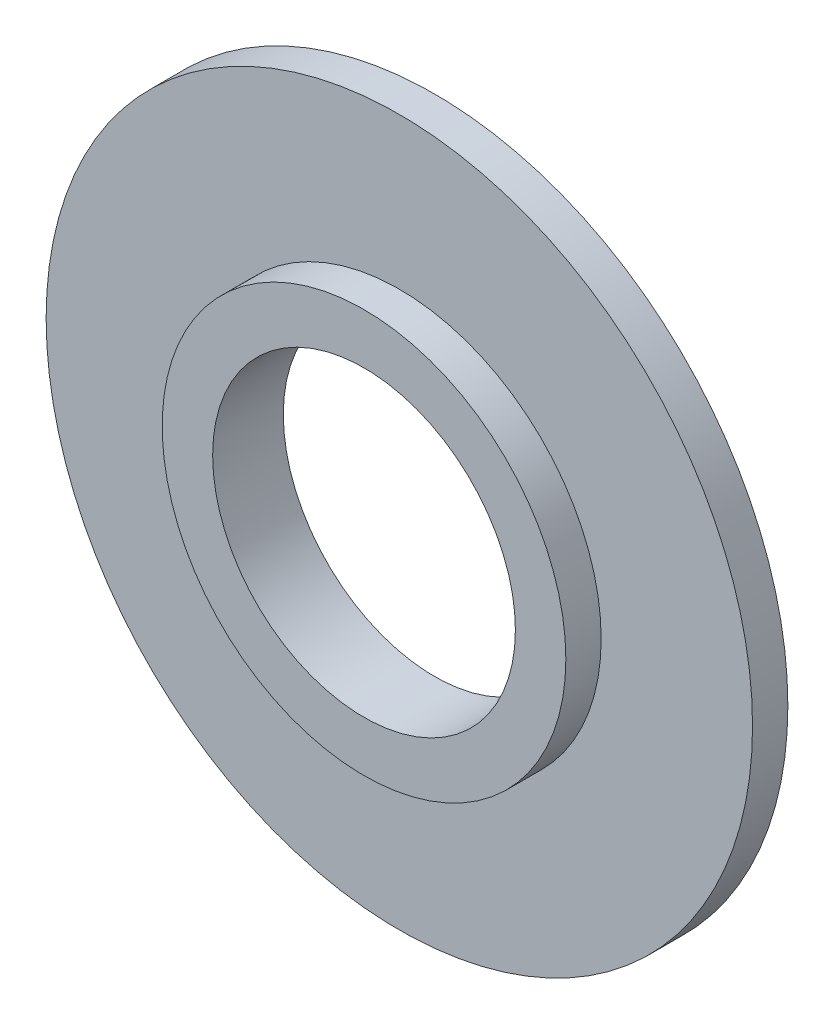
SolidWorks part; units mm, degrees
material "ABS"
ref_plane "前视基准面" through (0, 0, 0) normal (0, 0, 1) x (1, 0, 0)
ref_plane "上视基准面" through (0, 0, 0) normal (0, 1, 0) x (1, 0, 0)
ref_plane "右视基准面" through (0, 0, 0) normal (1, 0, 0) x (0, 0, -1)
other "Configuration Table"
sketch "草图1" plane through (0, 0, 0) normal (0, 0, 1) x (1, 0, 0)
  circle A0 centre (0, 0) radius 3
  circle A1 centre (0, 0) radius 4
  dimension "D1" = 6
  dimension "D2" = 8
extrude "凸台-拉伸1" add sketch "草图1" against normal blind 0.7
sketch "草图2" plane through (0, 0, -0.7) normal (0, 0, -1) x (-1, 0, 0)
  circle A0 centre (0, 0) radius 7
  circle A1 centre (0, 0) radius 3
  dimension "D1" = 14
  dimension "D2" = 6
extrude "凸台-拉伸2" add sketch "草图2" along normal blind 0.7
